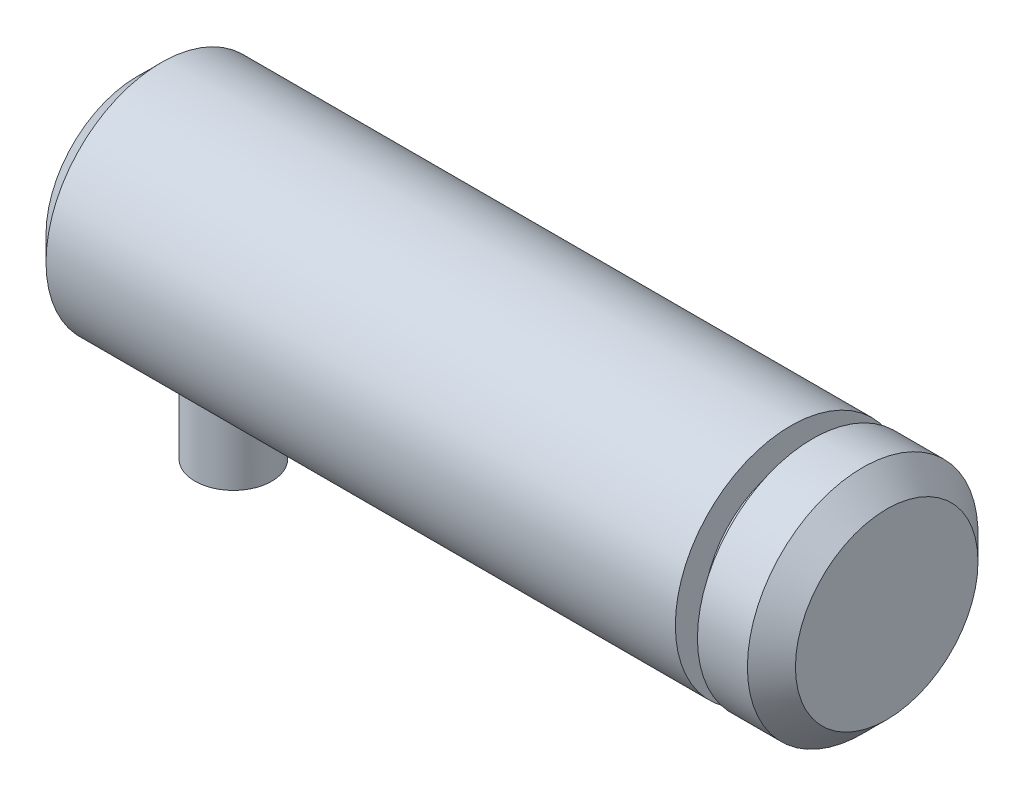
SolidWorks part; units mm, degrees
ref_plane "Front Plane" through (0, 0, 0) normal (0, 0, 1) x (1, 0, 0)
ref_plane "Top Plane" through (0, 0, 0) normal (0, 1, 0) x (1, 0, 0)
ref_plane "Right Plane" through (0, 0, 0) normal (1, 0, 0) x (0, 0, -1)
ref_plane "Plane1" through (0, 0, 0) normal (0, 0, 1) x (1, 0, 0)
sketch "Sketch1" plane through (0, 0, 0) normal (0, 0, 1) x (1, 0, 0)
  line L0 (-19.5, 0) -> (-19.5, 6)
  line L1 (-19.5, 6) -> (14.5, 6)
  line L2 (14.5, 6) -> (14.5, 0)
  line L3 (14.5, 0) -> (-19.5, 0)
  line L4 (14.5, 0) -> (-19.5, 0) construction
revolve "Revolve1" add sketch "Sketch1" angle 360 about L4
ref_plane "Plane2" through (0, 0, 0) normal (0, 0, 1) x (1, 0, 0)
sketch "Sketch2" plane through (0, 0, 0) normal (0, 0, 1) x (1, 0, 0)
  line L0 (-19.5, 4.75) -> (-18.25, 6)
  line L1 (-18.25, 6) -> (-19.5, 6)
  line L2 (-19.5, 6) -> (-19.5, 4.75)
  line L3 (29, 0) -> (-29, 0) construction
revolve "Cut-Revolve1" cut sketch "Sketch2" angle 360 about L3
ref_plane "Plane3" through (0, 0, 0) normal (0, 1, 0) x (1, 0, 0)
sketch "Sketch3" plane through (0, 0, 0) normal (0, 1, 0) x (1, 0, 0)
  circle A0 centre (-14.5, 0) radius 2
extrude "Boss-Extrude1" add sketch "Sketch3" against normal blind 10
ref_plane "Plane4" through (0, 0, 0) normal (0, 0, 1) x (1, 0, 0)
sketch "Sketch4" plane through (0, 0, 0) normal (0, 0, 1) x (1, 0, 0)
  line L0 (14.5, 0) -> (14.5, 6)
  line L1 (14.5, 6) -> (19.5, 6)
  line L2 (19.5, 6) -> (19.5, 0)
  line L3 (19.5, 0) -> (14.5, 0)
  line L4 (19.5, 0) -> (14.5, 0) construction
revolve "Revolve2" add sketch "Sketch4" angle 360 about L4
ref_plane "Plane5" through (0, 0, 0) normal (0, 0, 1) x (1, 0, 0)
sketch "Sketch5" plane through (0, 0, 0) normal (0, 0, 1) x (1, 0, 0)
  line L0 (14.5, 4.5) -> (15.65, 4.5)
  line L1 (15.65, 4.5) -> (15.65, 6)
  line L2 (15.65, 6) -> (14.5, 6)
  line L3 (14.5, 6) -> (14.5, 4.5)
  line L4 (29, 0) -> (-29, 0) construction
revolve "Cut-Revolve2" cut sketch "Sketch5" angle 360 about L4
ref_plane "Plane6" through (0, 0, 0) normal (0, 0, 1) x (1, 0, 0)
sketch "Sketch6" plane through (0, 0, 0) normal (0, 0, 1) x (1, 0, 0)
  line L0 (18.25, 6) -> (19.5, 4.75)
  line L1 (19.5, 4.75) -> (19.5, 6)
  line L2 (19.5, 6) -> (18.25, 6)
  line L3 (29, 0) -> (-29, 0) construction
revolve "Cut-Revolve3" cut sketch "Sketch6" angle 360 about L3
